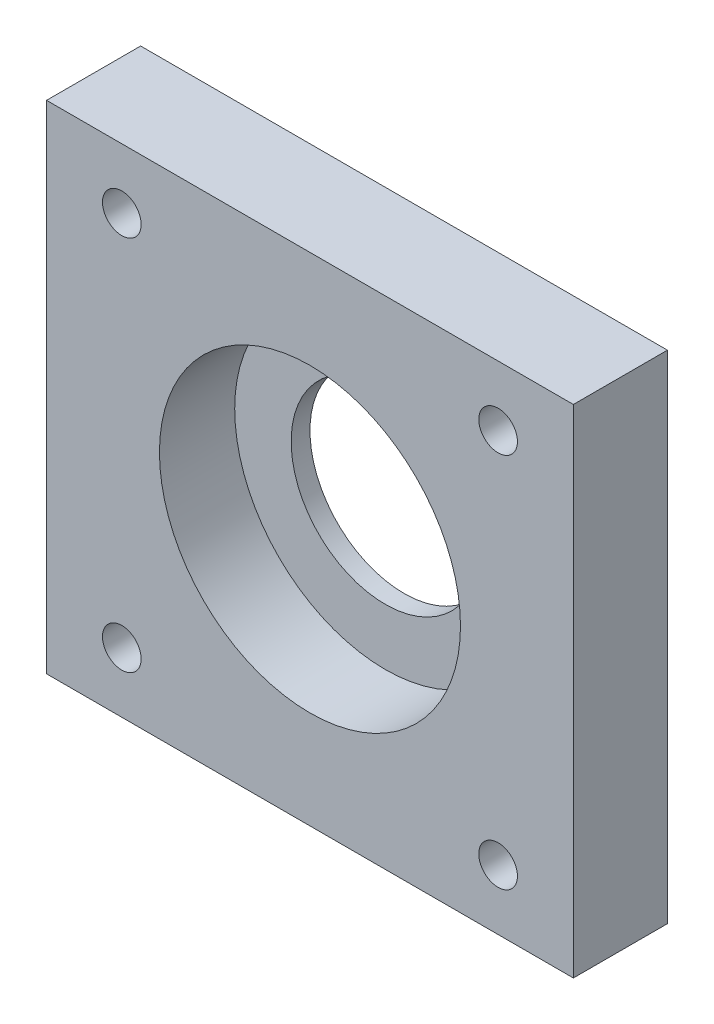
SolidWorks part; units mm, degrees
ref_plane "Front Plane" through (0, 0, 0) normal (0, 0, 1) x (1, 0, 0)
ref_plane "Top Plane" through (0, 0, 0) normal (0, 1, 0) x (1, 0, 0)
ref_plane "Right Plane" through (0, 0, 0) normal (1, 0, 0) x (0, 0, -1)
sketch "Sketch1" plane through (0, 0, 0) normal (0, 0, 1) x (1, 0, 0)
  line L1 (-44.45, 41.91) -> (44.45, 41.91)
  line L2 (-44.45, 41.91) -> (-44.45, -41.91)
  line L3 (-44.45, -41.91) -> (44.45, -41.91)
  line L4 (44.45, 41.91) -> (44.45, -41.91)
  line L5 (-44.45, 41.91) -> (44.45, -41.91) construction
  line L6 (-44.45, -41.91) -> (44.45, 41.91) construction
  point P0 (0, 0)
  dimension "D1" = 88.9
  dimension "D2" = 83.82
extrude "Boss-Extrude1" add sketch "Sketch1" along normal blind 15.875
sketch "Sketch2" plane through (0, 0, 15.875) normal (0, 0, 1) x (1, 0, 0)
  line L1 (-31.75, -31.75) -> (31.75, -31.75) construction
  line L2 (-31.75, -31.75) -> (-31.75, 31.75) construction
  line L3 (-31.75, 31.75) -> (31.75, 31.75) construction
  line L4 (31.75, -31.75) -> (31.75, 31.75) construction
  line L5 (-31.75, -31.75) -> (31.75, 31.75) construction
  line L6 (-31.75, 31.75) -> (31.75, -31.75) construction
  circle A0 centre (-31.75, 31.75) radius 3.2639
  circle A1 centre (31.75, 31.75) radius 3.2639
  circle A2 centre (31.75, -31.75) radius 3.2639
  circle A3 centre (-31.75, -31.75) radius 3.2639
  circle A4 centre (0, 0) radius 15.875
  point P0 (0, 0)
  dimension "D2" = 6.5278
  dimension "D3" = 31.75
  dimension "D1" = 63.5
extrude "Cut-Extrude1" cut sketch "Sketch2" against normal through all
sketch "Sketch3" plane through (0, 0, 15.875) normal (0, 0, 1) x (1, 0, 0)
  circle A0 centre (0, 0) radius 25.4
  dimension "D1" = 50.8
extrude "Cut-Extrude2" cut sketch "Sketch3" against normal blind 12.7
